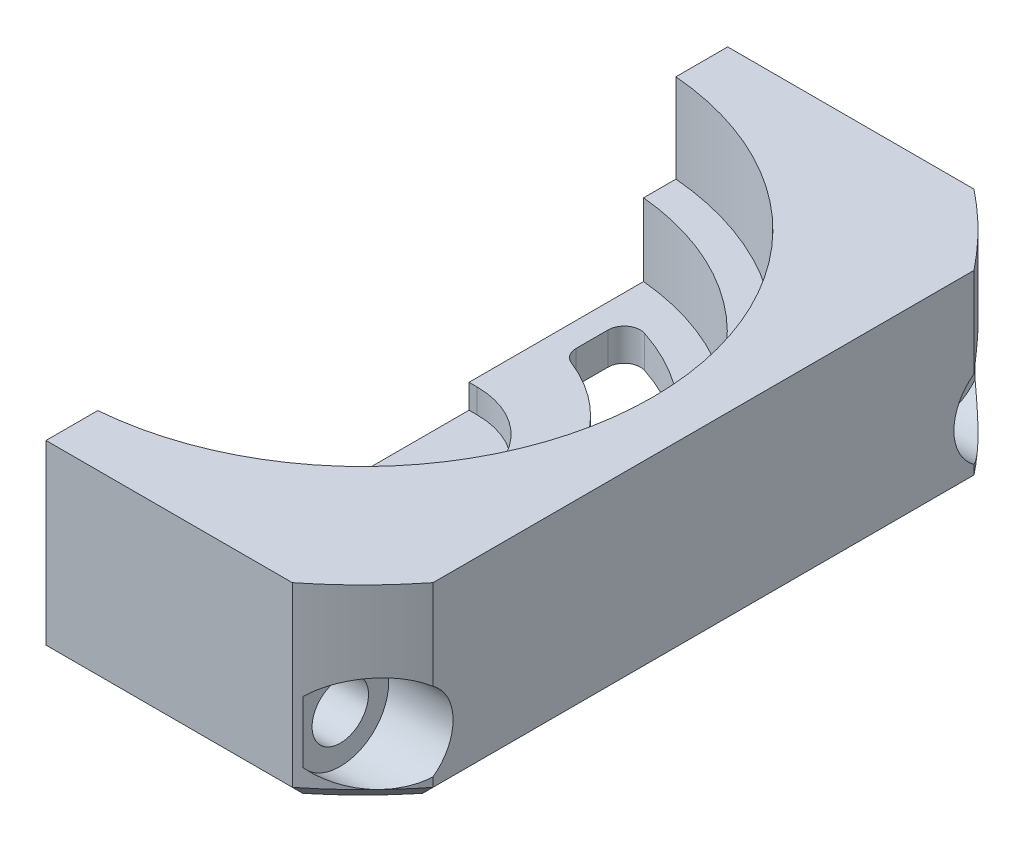
SolidWorks part; units mm, degrees
ref_plane "Front Plane" through (0, 0, 0) normal (0, 0, 1) x (1, 0, 0)
ref_plane "Top Plane" through (0, 0, 0) normal (0, 1, 0) x (1, 0, 0)
ref_plane "Right Plane" through (0, 0, 0) normal (1, 0, 0) x (0, 0, -1)
sketch "Sketch2" plane through (0, 0, 0) normal (0, 1, 0) x (1, 0, 0)
  line L1 (-21.15, 21.15) -> (21.15, 21.15)
  line L2 (-21.15, 21.15) -> (-21.15, -21.15)
  line L3 (-21.15, -21.15) -> (21.15, -21.15)
  line L4 (21.15, 21.15) -> (21.15, -21.15)
  line L5 (-21.15, 21.15) -> (21.15, -21.15) construction
  line L6 (-21.15, -21.15) -> (21.15, 21.15) construction
  point P0 (0, 0)
  dimension "D1" = 42.3
extrude "Boss-Extrude1" add sketch "Sketch2" along normal blind 12
sketch "Sketch5" plane through (0, 12, 0) normal (0, 1, 0) x (1, 0, 0)
  circle A0 centre (0, 0) radius 27
  circle A1 centre (0, 0) radius 29.9106
  dimension "D1" = 54
extrude "Cut-Extrude4" cut sketch "Sketch5" against normal through all
sketch "Sketch6" plane through (0, 12, 0) normal (0, 1, 0) x (1, 0, 0)
  line L9 (0, 18) -> (-21.15, 18)
  line L10 (-21.15, 18) -> (-21.15, -18)
  line L11 (-21.15, 16.7833) -> (-21.15, -16.7833) construction
  line L24 (-21.15, -18) -> (0, -18)
  arc A0 (0, 18) -> (0, -18) centre (0, 0) cw
  circle A3 centre (0, 0) radius 11 construction
  arc A6 (0, -18) -> (0, 18) centre (0, 0) ccw
  point P8 (-21.15, 18)
  dimension "D3" = 18
  dimension "D5" = 22
extrude "Cut-Extrude5" cut sketch "Sketch6" against normal offset from surface (10 mm away) 2
sketch "Sketch7" plane through (0, 2, 0) normal (0, 1, 0) x (1, 0, 0)
  line L0 (-2, 0) -> (2, 0) construction
  line L1 (-2, 5.1) -> (2, 5.1)
  line L2 (-2, -5.1) -> (2, -5.1)
  arc A0 (-2, 5.1) -> (-2, -5.1) centre (-2, 0) ccw
  arc A1 (2, -5.1) -> (2, 5.1) centre (2, 0) ccw
  point P2 (0, 0)
  point P8 (3.5809, 0)
  point P9 (0, 0)
  point P10 (2.3479, 0)
  dimension "D1" = 5.1
  dimension "D2" = 4
extrude "Cut-Extrude6" cut sketch "Sketch7" against normal blind 1.5
sketch "Sketch8" plane through (0, 2, 0) normal (0, 1, 0) x (1, 0, 0)
  line L0 (0, 16) -> (-21.15, 16)
  line L1 (0, -16) -> (-21.15, -16)
  line L2 (-21.15, -16) -> (-21.15, -16.7833)
  line L3 (-21.15, 16.7833) -> (-21.15, -16.7833)
  line L4 (-21.15, 16.7833) -> (-21.15, 16)
  line L5 (-20.1246, -18) -> (0, -18)
  line L6 (-20.1246, -18) -> (0, -18)
  line L8 (0, 18) -> (-20.1246, 18)
  line L10 (0, 18) -> (-20.1246, 18)
  arc A0 (0, -16) -> (0, 16) centre (0, 0) ccw
  arc A3 (-20.1246, 18) -> (-21.15, 16.7833) centre (0, 0) ccw
  arc A4 (0, -18) -> (0, 18) centre (0, 0) ccw
  arc A6 (0, -18) -> (0, 18) centre (0, 0) ccw
  arc A8 (-20.1246, 18) -> (-21.15, 16.7833) centre (0, 0) ccw
  arc A9 (-21.15, -16.7833) -> (-20.1246, -18) centre (0, 0) ccw
  arc A10 (-21.15, -16.7833) -> (-20.1246, -18) centre (0, 0) ccw
  point P1 (0, 0)
  point P13 (0.4216, 0)
  dimension "D1" = 32
  dimension "D2" = 0
extrude "Boss-Extrude2" add sketch "Sketch8" along normal offset from surface (4.5 mm away) 5.5 up to face at (2.0167, 12, 0)
sketch "Sketch13" plane through (0, 12, 0) normal (0, 1, 0) x (1, 0, 0)
  line L0 (-16.7833, -21.15) -> (16.7833, -21.15) construction
  line L1 (-21.15, 21.15) -> (1.5, 21.15)
  line L2 (-21.15, 21.15) -> (-21.15, -21.15)
  line L3 (-21.15, -21.15) -> (1.5, -21.15)
  line L4 (1.5, 21.15) -> (1.5, -21.15)
  line L5 (16.7833, 21.15) -> (-16.7833, 21.15) construction
  line L6 (-21.15, -16) -> (-21.15, 16) construction
  point P8 (-3.1741, 21.15)
  dimension "D1" = 1.5
extrude "Cut-Extrude9" cut sketch "Sketch13" against normal through all
chamfer "Chamfer4" distance 1 angle 45 5 edges at (19.0919, 0, 19.0919) (9.1416, 0, 21.15) (9.1416, 0, -21.15) (19.0919, 0, -19.0919) (21.15, 0, 0)
sketch "Sketch11" plane through (0, 2, 0) normal (0, 1, 0) x (1, 0, 0)
  line L2 (1.5, 0) -> (21.15, 0) construction
  line L3 (1.5, -15.9295) -> (1.5, -5.1) construction
  line L4 (21.15, -16.7833) -> (21.15, 16.7833) construction
  line L5 (3, 13.5394) -> (3, 9.5394)
  line L6 (3, -9.5394) -> (3, -13.5394)
  line L14 (1.5, -5.1) -> (1.5, 5.1) construction
  line L16 (1.5, 5.1) -> (1.5, 15.9295) construction
  arc A3 (3, 9.5394) -> (3, -9.5394) centre (0, 0) cw
  arc A4 (3, -13.5394) -> (3, 13.5394) centre (0, 0) ccw
  point P0 (3, -12.3522)
  point P6 (10, 0)
  dimension "D1" = 4
  dimension "D3" = 10
  dimension "D2" = 1.5
extrude "Cut-Extrude8" cut sketch "Sketch11" against normal through all
fillet "Fillet12" radius 1 4 edges at (3, 1, 9.5394) (3, 1, -13.5394) (3, 1, 13.5394) (3, 1, -9.5394)
sketch "Sketch14" plane through (1.5, 0, 0) normal (-1, 0, 0) x (0, 0, 1)
  line L0 (-18.5398, 4) -> (18.5398, 4) construction
  line L1 (20.15, 0) -> (-20.15, 0) construction
  line L2 (-15.9295, 2) -> (-21.15, 2) construction
  line L3 (-21.15, 1) -> (-21.15, 12) construction
  line L4 (-18.5398, 4) -> (-18.5398, 2) construction
  line L5 (15.9295, 2) -> (21.15, 2) construction
  line L6 (21.15, 1) -> (21.15, 12) construction
  line L7 (18.5398, 2) -> (18.5398, 4) construction
  circle A0 centre (-18.5398, 4) radius 1.75
  circle A1 centre (18.5398, 4) radius 1.75
  point P14 (18.5398, 5)
  point P20 (18.3869, 5)
  dimension "D1" = 4
  dimension "D2" = 3.5
extrude "Cut-Extrude10" cut sketch "Sketch14" against normal through all and the other way through all
ref_plane "Plane1" through (21.5, 0, 0) normal (-1, 0, 0) x (0, 0, 1)
sketch "Sketch15" plane through (21.15, 0, 0) normal (1, 0, 0) x (0, 0, -1)
  circle A0 centre (-18.5398, 4) radius 3
  circle A1 centre (18.5398, 4) radius 3
  point P5 (18.6698, 5)
  point P6 (18.5398, 5)
  dimension "D1" = 6
  dimension "D2" = 6
extrude "Cut-Extrude11" cut sketch "Sketch15" against normal blind 4
